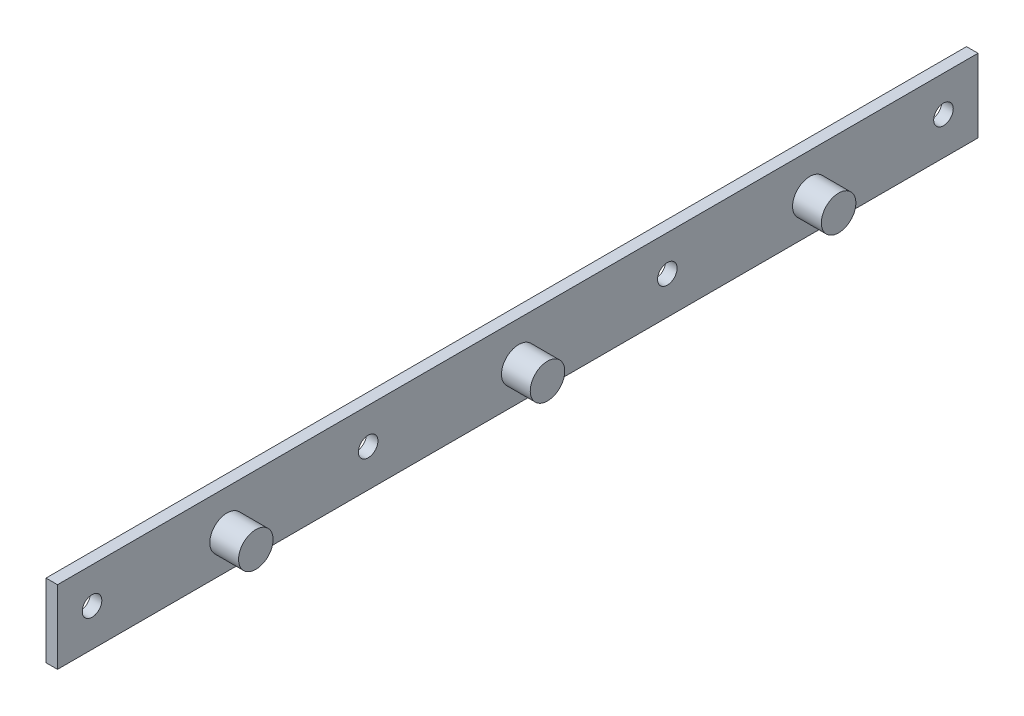
SolidWorks part; units mm, degrees
ref_plane "Plano frontal" through (0, 0, 0) normal (0, 0, 1) x (1, 0, 0)
ref_plane "Plano superior" through (0, 0, 0) normal (0, 1, 0) x (1, 0, 0)
ref_plane "Plano direito" through (0, 0, 0) normal (1, 0, 0) x (0, 0, -1)
sketch "Esboço1" plane through (0, 0, 0) normal (1, 0, 0) x (0, 0, -1)
  line L1 (-80, -6.375) -> (80, -6.375)
  line L2 (-80, -6.375) -> (-80, 6.375)
  line L3 (-80, 6.375) -> (80, 6.375)
  line L4 (80, -6.375) -> (80, 6.375)
  line L5 (-80, -6.375) -> (80, 6.375) construction
  line L6 (-80, 6.375) -> (80, -6.375) construction
  circle A0 centre (-74, 0.175) radius 1.7
  circle A1 centre (-26, 0.175) radius 1.7
  circle A2 centre (26, 0.175) radius 1.7
  circle A3 centre (74, 0.175) radius 1.7
  point P0 (0, 0)
  dimension "D1" = 160
  dimension "D4" = 6.55
  dimension "D3" = 3.4
  dimension "D5" = 52
  dimension "D6" = 54
  dimension "D7" = 54
  dimension "D8" = 48
  dimension "D9" = 48
  dimension "D2" = 12.75
extrude "Ressalto-extrusão1" add sketch "Esboço1" along normal blind 2
sketch "Esboço2" plane through (2, 0, 0) normal (1, 0, 0) x (0, 0, -1)
  line L1 (80, -6.375) -> (80, 6.375) construction
  line L2 (-80, -6.375) -> (80, -6.375) construction
  circle A0 centre (0.17, -0.555) radius 3
  circle A1 centre (50.77, -0.555) radius 3
  circle A2 centre (-50.53, -0.555) radius 3
  dimension "D1" = 50.7
  dimension "D2" = 50.6
  dimension "D3" = 79.83
  dimension "D4" = 5.82
extrude "Ressalto-extrusão2" add sketch "Esboço2" along normal blind 5
